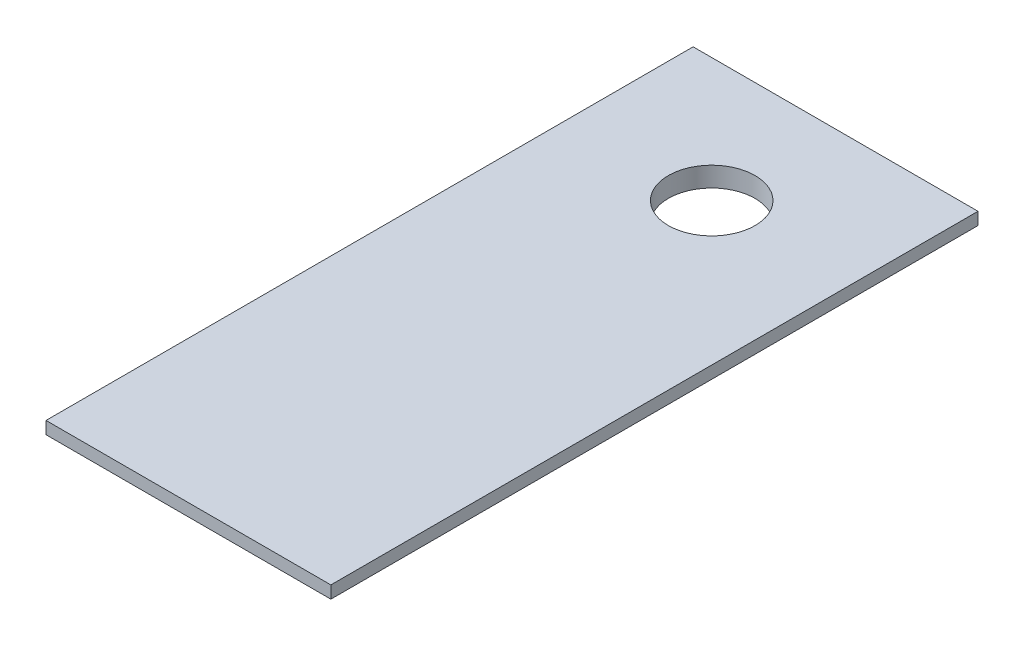
SolidWorks part; units mm, degrees
ref_plane "Front" through (0, 0, 0) normal (0, 0, 1) x (1, 0, 0)
ref_plane "Top" through (0, 0, 0) normal (0, 1, 0) x (1, 0, 0)
ref_plane "Right" through (0, 0, 0) normal (1, 0, 0) x (0, 0, -1)
sketch "Sketch1" plane through (0, 7.5, 0) normal (0, 1, 0) x (1, 0, 0)
  line L1 (0, 50) -> (20, 50)
  line L2 (0, 50) -> (0, 0.75)
  line L3 (0, 0.75) -> (20, 0.75)
  line L4 (20, 50) -> (20, 0.75)
  line L5 (0, 50) -> (20, 0.75) construction
  line L6 (0, 0.75) -> (20, 50) construction
  point P4 (10, 25.375)
extrude "Boss-Extrude1" add sketch "Sketch1" against normal blind 0.6
sketch "Sketch2" plane through (0, 7.5, 0) normal (0, 1, 0) x (1, 0, 0)
  line L1 (-1.5, 51.5) -> (21.5, 51.5)
  line L2 (-1.5, 51.5) -> (-1.5, -0.75)
  line L3 (-1.5, -0.75) -> (21.5, -0.75)
  line L4 (21.5, 51.5) -> (21.5, -0.75)
  line L5 (-1.5, 51.5) -> (21.5, -0.75) construction
  line L6 (-1.5, -0.75) -> (21.5, 51.5) construction
  point P4 (10, 25.375)
extrude "Boss-Extrude2" add sketch "Sketch2" along normal blind 1
sketch "Sketch3" plane through (0, 8.5, 0) normal (0, 1, 0) x (1, 0, 0)
  line L1 (10, 51.5) -> (10, 31.5) construction
  line L2 (21.5, 51.5) -> (-1.5, 51.5) construction
  circle A0 centre (10, 41.5) radius 3.5
  point P6 (0, 0)
  point P7 (10, 37.6554)
  dimension "D1" = 10
  dimension "D2" = 7
extrude "Cut-Extrude1" cut sketch "Sketch3" against normal blind 10
